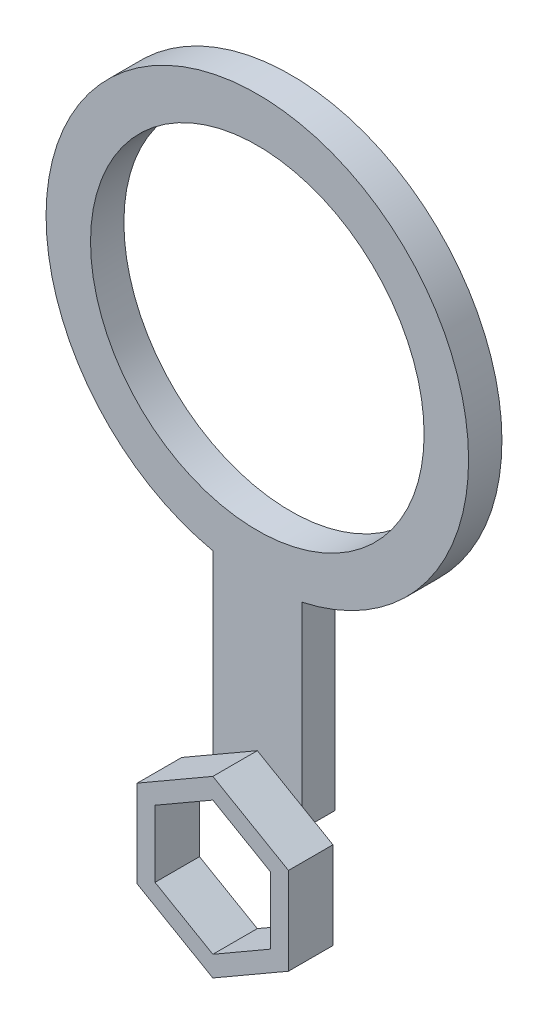
SolidWorks part; units mm, degrees
ref_plane "Front Plane" through (0, 0, 0) normal (0, 0, 1) x (1, 0, 0)
ref_plane "Top Plane" through (0, 0, 0) normal (0, 1, 0) x (1, 0, 0)
ref_plane "Right Plane" through (0, 0, 0) normal (1, 0, 0) x (0, 0, -1)
sketch "Sketch1" plane through (0, 0, 0) normal (0, 0, 1) x (1, 0, 0)
  line L0 (0, 0) -> (0, 40) construction
  line L1 (0, 5.7735) -> (-5, 2.8868)
  line L2 (-5, 2.8868) -> (-5, -2.8868)
  line L3 (-5, -2.8868) -> (0, -5.7735)
  line L4 (0, -5.7735) -> (5, -2.8868)
  line L5 (5, -2.8868) -> (5, 2.8868)
  line L6 (5, 2.8868) -> (0, 5.7735)
  line L7 (-4, 3.4641) -> (-4, 21.4258)
  line L8 (4, 3.4641) -> (4, 21.4258)
  line L9 (4, 3.4641) -> (-4, 3.4641) construction
  circle A0 centre (0, 0) radius 5 construction
  circle A1 centre (0, 40) radius 15
  circle A2 centre (0, 40) radius 19
  point P1 (5, 0)
  dimension "D2" = 30
  dimension "D3" = 4
  dimension "D1" = 10
  dimension "D4" = 8
  dimension "D5" = 40
extrude "Boss-Extrude1" add sketch "Sketch1" along normal blind 3 contours L5 L6 L1 L2 L3 L4 | A2 L7 L1 L6 L8 | A2 A1
sketch "Sketch2" plane through (0, 0, 3) normal (0, 0, 1) x (1, 0, 0)
  line L0 (0, 0) -> (0, -7.852) construction
  line L1 (0, -6.0044) -> (5.2, -3.0022)
  line L2 (5.2, -3.0022) -> (5.2, 3.0022)
  line L3 (5.2, 3.0022) -> (0, 6.0044)
  line L4 (0, 6.0044) -> (-5.2, 3.0022)
  line L5 (-5.2, 3.0022) -> (-5.2, -3.0022)
  line L6 (-5.2, -3.0022) -> (0, -6.0044)
  line L7 (0, -7.852) -> (6.8, -3.926)
  line L8 (6.8, -3.926) -> (6.8, 3.926)
  line L9 (6.8, 3.926) -> (0, 7.852)
  line L10 (0, 7.852) -> (-6.8, 3.926)
  line L11 (-6.8, 3.926) -> (-6.8, -3.926)
  line L12 (-6.8, -3.926) -> (0, -7.852)
  line L13 (5, -2.8868) -> (5, 2.8868) construction
  circle A0 centre (0, 0) radius 5.2 construction
  circle A1 centre (0, 0) radius 6.8 construction
  point P1 (0, 0)
  dimension "D1" = 0.2
  dimension "D2" = 1.6
extrude "Boss-Extrude2" add sketch "Sketch2" along normal blind 4
sketch "Sketch3" plane through (0, 0, 3) normal (0, 0, 1) x (1, 0, 0)
  line L10 (4, 3.4641) -> (4, 3.695)
  line L11 (4, 3.695) -> (0, 6.0044)
  line L12 (0, 6.0044) -> (-4, 3.695)
  line L13 (-4, 3.695) -> (-4, 3.4641)
  line L14 (-4, 3.4641) -> (-5, 2.8868)
  line L15 (-5, 2.8868) -> (-5, -2.8868)
  line L16 (-5, -2.8868) -> (0, -5.7735)
  line L17 (0, -5.7735) -> (5, -2.8868)
  line L18 (5, -2.8868) -> (5, 2.8868)
  line L19 (5, 2.8868) -> (4, 3.4641)
  line L20 (4, 3.4641) -> (4, 3.695)
  line L21 (4, 3.695) -> (0, 6.0044)
  line L22 (0, 6.0044) -> (-4, 3.695)
  line L23 (-4, 3.695) -> (-4, 3.4641)
  line L24 (-4, 3.4641) -> (-5, 2.8868)
  line L25 (-5, 2.8868) -> (-5, -2.8868)
  line L26 (-5, -2.8868) -> (0, -5.7735)
  line L27 (0, -5.7735) -> (5, -2.8868)
  line L28 (5, -2.8868) -> (5, 2.8868)
  line L29 (5, 2.8868) -> (4, 3.4641)
  dimension "D1" = 0
extrude "Cut-Extrude1" cut sketch "Sketch3" against normal through all
